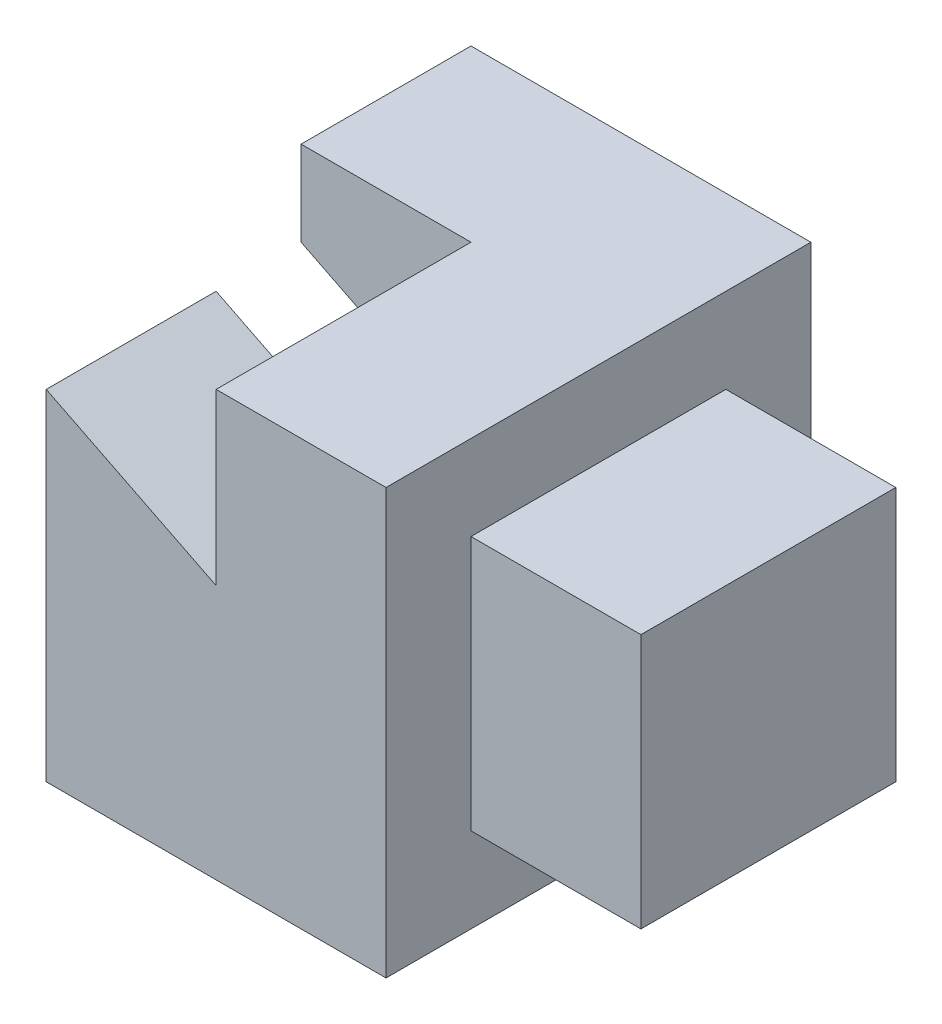
SolidWorks part; units mm, degrees
ref_plane "Front Plane" through (0, 0, 0) normal (0, 0, 1) x (1, 0, 0)
ref_plane "Top Plane" through (0, 0, 0) normal (0, 1, 0) x (1, 0, 0)
ref_plane "Right Plane" through (0, 0, 0) normal (1, 0, 0) x (0, 0, -1)
sketch "Sketch1" plane through (0, 0, 0) normal (1, 0, 0) x (0, 0, -1)
  line L1 (-1.5, -1.5) -> (1.5, -1.5)
  line L2 (-1.5, -1.5) -> (-1.5, 1.5)
  line L3 (-1.5, 1.5) -> (1.5, 1.5)
  line L4 (1.5, -1.5) -> (1.5, 1.5)
  line L5 (-1.5, -1.5) -> (1.5, 1.5) construction
  line L6 (-1.5, 1.5) -> (1.5, -1.5) construction
  point P0 (0, 0)
  dimension "D1" = 3
  dimension "D2" = 3
extrude "Boss-Extrude1" add sketch "Sketch1" along normal blind 2
sketch "Sketch2" plane through (0, 0, 0) normal (-1, 0, 0) x (0, 0, 1)
  line L1 (-2.5, -2.5) -> (2.5, -2.5)
  line L2 (-2.5, -2.5) -> (-2.5, 2.5)
  line L3 (-2.5, 2.5) -> (2.5, 2.5)
  line L4 (2.5, -2.5) -> (2.5, 2.5)
  line L5 (-2.5, -2.5) -> (2.5, 2.5) construction
  line L6 (-2.5, 2.5) -> (2.5, -2.5) construction
  point P0 (0, 0)
  dimension "D1" = 5
  dimension "D2" = 5
extrude "Boss-Extrude2" add sketch "Sketch2" along normal blind 2
sketch "Sketch4" plane through (0, 0, 2.5) normal (0, 0, 1) x (1, 0, 0)
  line L0 (-2, -2.5) -> (-4, -2.5)
  line L1 (-4, -2.5) -> (-4, 1.5)
  line L2 (-4, 1.5) -> (-2, 0.5)
  line L3 (-2, -2.5) -> (-2, 2.5) construction
  line L4 (-2, 0.5) -> (-2, -2.5)
  dimension "D1" = 3
  dimension "D2" = 4
  dimension "D3" = 2
extrude "Boss-Extrude3" add sketch "Sketch4" against normal blind 2
sketch "Sketch5" plane through (0, 0, -2.5) normal (0, 0, -1) x (-1, 0, 0)
  line L0 (2, 2.5) -> (2, 0.5)
  line L1 (2, 0.5) -> (4, 1.5)
  line L2 (4, 1.5) -> (4, 2.5)
  line L3 (4, 2.5) -> (2, 2.5)
extrude "Boss-Extrude4" add sketch "Sketch5" against normal blind 2
